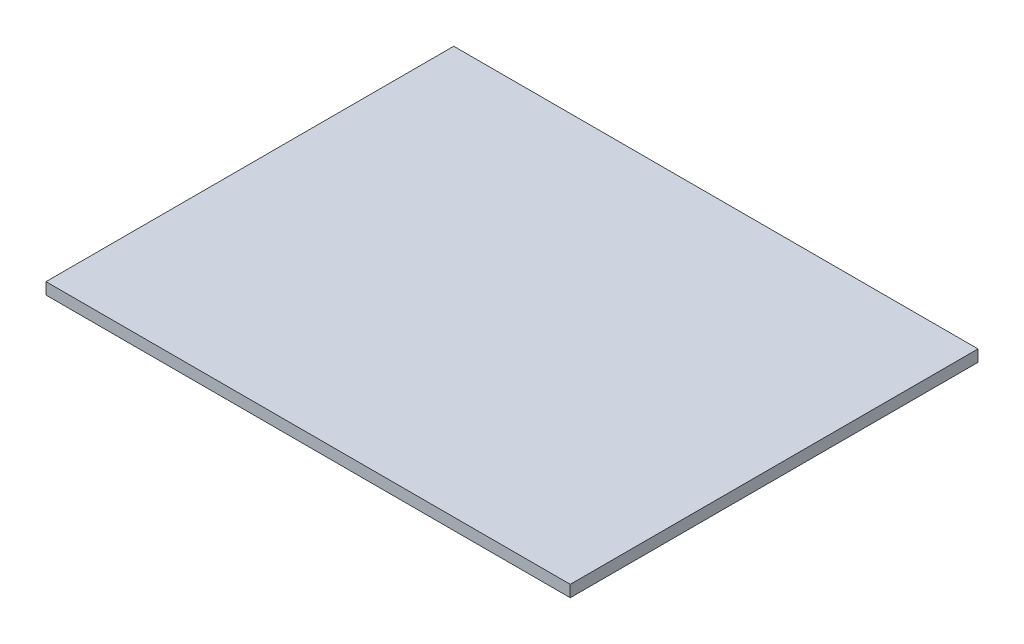
SolidWorks part; units mm, degrees
ref_plane "Alzado" through (0, 0, 0) normal (0, 0, 1) x (1, 0, 0)
ref_plane "Planta" through (0, 0, 0) normal (0, 1, 0) x (1, 0, 0)
ref_plane "Vista lateral" through (0, 0, 0) normal (1, 0, 0) x (0, 0, -1)
sketch "Croquis2" plane through (0, 0, 0) normal (0, 1, 0) x (1, 0, 0)
  line L1 (-45, 35) -> (45, 35)
  line L2 (-45, 35) -> (-45, -35)
  line L3 (-45, -35) -> (45, -35)
  line L4 (45, 35) -> (45, -35)
  line L5 (-45, 35) -> (45, -35) construction
  line L6 (-45, -35) -> (45, 35) construction
  point P0 (0, 0)
  dimension "D1" = 70
  dimension "D2" = 90
extrude "Saliente-Extruir1" add sketch "Croquis2" along normal blind 2
